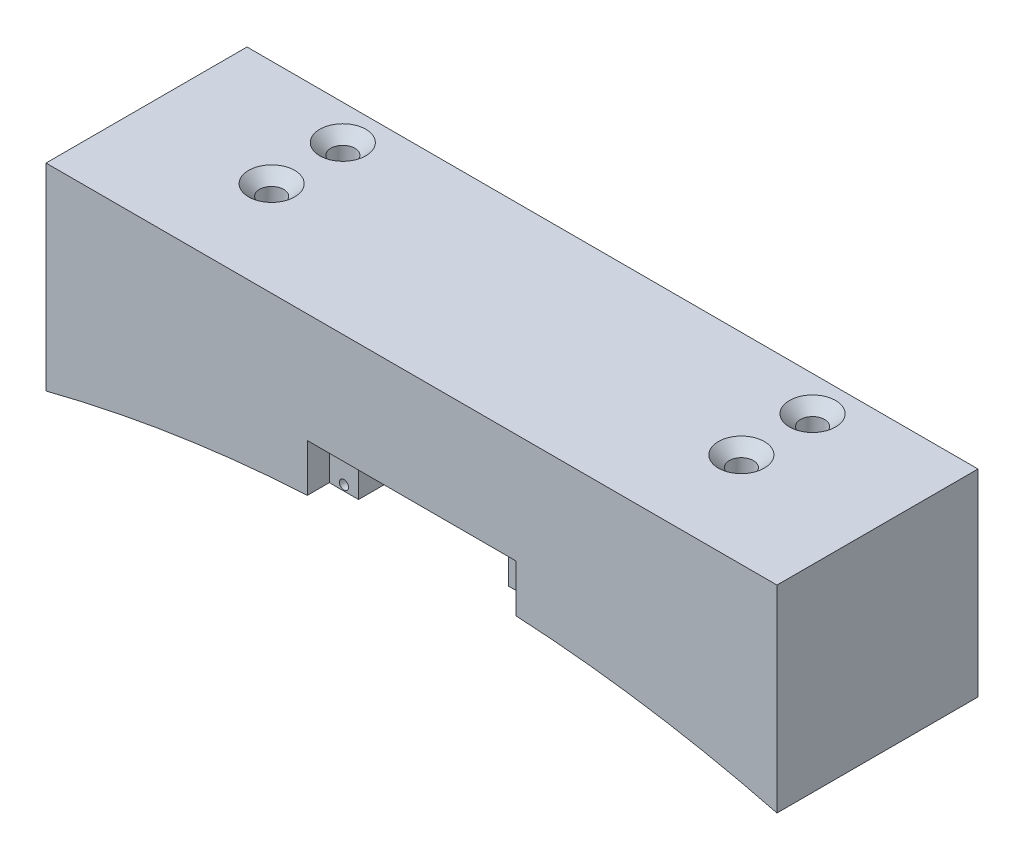
SolidWorks part; units mm, degrees
ref_plane "Front Plane" through (0, 0, 0) normal (0, 0, 1) x (1, 0, 0)
ref_plane "Top Plane" through (0, 0, 0) normal (0, 1, 0) x (1, 0, 0)
ref_plane "Right Plane" through (0, 0, 0) normal (1, 0, 0) x (0, 0, -1)
sketch "Sketch1" plane through (0, 0, 0) normal (0, 1, 0) x (1, 0, 0)
  line L1 (-100, -27.5) -> (100, -27.5)
  line L2 (-100, -27.5) -> (-100, 27.5)
  line L3 (-100, 27.5) -> (100, 27.5)
  line L4 (100, -27.5) -> (100, 27.5)
  line L5 (-100, -27.5) -> (100, 27.5) construction
  line L6 (-100, 27.5) -> (100, -27.5) construction
  point P0 (0, 0)
  dimension "D1" = 200
  dimension "D2" = 55
extrude "Boss-Extrude1" add sketch "Sketch1" along normal blind 30
sketch "Sketch2" plane through (0, 0, 0) normal (0, -1, 0) x (1, 0, 0)
  line L0 (0, 27.5) -> (0, -36.2844) construction
  line L1 (-28.5, 1.4842) -> (-20.5, 1.4842)
  line L2 (-28.5, 1.4842) -> (-28.5, 21.4842)
  line L3 (-28.5, 21.4842) -> (-20.5, 21.4842)
  line L4 (-20.5, 1.4842) -> (-20.5, 21.4842)
  line L5 (-28.5, 1.4842) -> (-20.5, 21.4842) construction
  line L6 (-28.5, 21.4842) -> (-20.5, 1.4842) construction
  line L7 (-100, 27.5) -> (100, 27.5) construction
  line L8 (28.5, 21.4842) -> (20.5, 1.4842) construction
  line L9 (28.5, 1.4842) -> (20.5, 21.4842) construction
  line L10 (20.5, 1.4842) -> (20.5, 21.4842)
  line L11 (28.5, 21.4842) -> (20.5, 21.4842)
  line L12 (28.5, 1.4842) -> (28.5, 21.4842)
  line L13 (28.5, 1.4842) -> (20.5, 1.4842)
  point P0 (-24.5, 11.4842)
  point P14 (24.5, 11.4842)
  dimension "D1" = 8
  dimension "D2" = 20
  dimension "D3" = 20.5
extrude "Boss-Extrude2" add sketch "Sketch2" along normal blind 13
sketch "Sketch4" plane through (0, 0, 21.4842) normal (0, 0, 1) x (1, 0, 0)
  line L0 (-24.5, -13) -> (-24.5, 0) construction
  line L1 (-20.5, -13) -> (-28.5, -13) construction
  line L2 (-20.5, 0) -> (-28.5, 0) construction
  line L3 (24.5, -13) -> (24.5, 0) construction
  line L4 (28.5, -13) -> (20.5, -13) construction
  line L5 (28.5, 0) -> (20.5, 0) construction
sketch "Sketch6" plane through (0, 0, 21.4842) normal (0, 0, 1) x (1, 0, 0)
  line L0 (-28.5, -6.5) -> (-20.5, -6.5) construction
  line L1 (-28.5, -13) -> (-28.5, 0) construction
  line L2 (-20.5, -13) -> (-20.5, 0) construction
  line L3 (20.5, -13) -> (20.5, 0) construction
  line L4 (20.5, -6.5) -> (28.5, -6.5) construction
  line L5 (28.5, -13) -> (28.5, 0) construction
sketch "Sketch7" plane through (0, 0, 21.4842) normal (0, 0, 1) x (1, 0, 0)
  line L0 (-24.5, -13) -> (-24.5, 0) construction
  line L2 (-100, 0) -> (100, 0) construction
  circle A0 centre (-24.5, -1.5) radius 1.25
  circle A1 centre (-24.5, -11.5) radius 1.25
  point P10 (0, 0)
  point P12 (0, 0)
  dimension "D3" = 2.5
  dimension "D4" = 2.5
  dimension "D1" = 10
  dimension "D7" = 1.5
extrude "Cut-Extrude1" cut sketch "Sketch7" against normal through all
sketch "Sketch10" plane through (0, 0, 0) normal (0, -1, 0) x (-1, 0, 0)
  line L0 (0, -27.5) -> (0, 30.005) construction
  line L1 (100, -27.5) -> (-100, -27.5) construction
sketch "Sketch11" plane through (0, 0, 21.4842) normal (0, 0, 1) x (1, 0, 0)
  line L0 (24.5, -13) -> (24.5, 0) construction
  line L1 (28.5, 0) -> (20.5, 0) construction
  circle A0 centre (24.5, -1.5) radius 1.25
  circle A1 centre (24.5, -11.5) radius 1.25
  dimension "D1" = 10
  dimension "D2" = 1.5
extrude "Cut-Extrude2" cut sketch "Sketch11" against normal blind 13
sketch "Sketch13" plane through (0, 0, 0) normal (0, -1, 0) x (1, 0, 0)
  line L0 (100, -27.5) -> (-100, -27.5) construction
  line L1 (-100, 27.5) -> (-28.4968, 27.5)
  line L2 (-100, 27.5) -> (-100, -27.5)
  line L3 (-100, -27.5) -> (-28.4968, -27.5)
  line L4 (-28.4968, 27.5) -> (-28.4968, -27.5)
  line L6 (100, 27.5) -> (28.5439, 27.5)
  line L7 (100, 27.5) -> (100, -27.5)
  line L8 (100, -27.5) -> (28.5439, -27.5)
  line L9 (28.5439, 27.5) -> (28.5439, -27.5)
extrude "Boss-Extrude3" add sketch "Sketch13" along normal blind 13
sketch "Sketch16" plane through (0, -13, 0) normal (0, -1, 0) x (-1, 0, 0)
  line L0 (-64.272, -27.5) -> (-64.272, 31.589) construction
  line L1 (-100, -27.5) -> (-28.5439, -27.5) construction
  line L2 (64.2484, -27.5) -> (64.2484, 31.589) construction
  line L3 (28.4968, -27.5) -> (100, -27.5) construction
  circle A0 centre (-64.272, 17.9587) radius 3
  circle A1 centre (-64.272, -1.5196) radius 3
  circle A2 centre (64.2484, 17.9587) radius 3
  circle A3 centre (64.2484, -1.5196) radius 3
  dimension "D1" = 6
  dimension "D2" = 6
  dimension "D3" = 6
  dimension "D4" = 6
sketch "Sketch24" plane through (0, 0, 27.5) normal (0, 0, 1) x (1, 0, 0)
  line L0 (100, -13) -> (28.5439, -13)
  line L1 (-28.4968, -13) -> (-100, -13)
  arc A2 (-100, -13) -> (-28.4968, -13) centre (-64.2484, -13) cw
  arc A3 (28.5439, -13) -> (100, -13) centre (64.272, -13) cw
sketch "Sketch26" plane through (0, 0, 27.5) normal (0, 0, 1) x (1, 0, 0)
  line L0 (100, -24.0218) -> (100, -13)
  line L1 (0, 0) -> (0, 30) construction
  line L2 (-100, 30) -> (100, 30) construction
  line L3 (100, -13) -> (28.5439, -13)
  line L4 (-100, -24.0218) -> (-100, -13)
  line L5 (-100, -13) -> (-28.5439, -13)
  arc A0 (28.5439, -13) -> (100, -24.0218) centre (8.3729, -380.9147) cw
  arc A1 (-28.5439, -13) -> (-100, -24.0218) centre (-8.3729, -380.9147) ccw
extrude "Boss-Extrude4" add sketch "Sketch26" against normal through all
sketch "Sketch27" plane through (0, 0, 27.5) normal (0, 0, 1) x (1, 0, 0)
  line L0 (0.0235, 0) -> (0, 30) construction
  line L1 (-28.4968, 0) -> (28.5439, 0) construction
  line L2 (-100, 30) -> (100, 30) construction
sketch "Sketch17" plane through (0, 30, 0) normal (0, 1, 0) x (1, 0, 0)
  line L0 (-100, 0) -> (100, 0) construction
  line L1 (-100, 27.5) -> (-100, -27.5) construction
  line L2 (100, -27.5) -> (100, 27.5) construction
sketch "Sketch22" plane through (0, 30, 0) normal (0, 1, 0) x (1, 0, 0)
  circle A0 centre (64.272, 17.9587) radius 3
  circle A1 centre (-64.2484, 17.9587) radius 3
  circle A2 centre (-64.2484, -1.5196) radius 3
  circle A3 centre (64.272, -1.5196) radius 3
hole_wizard "CSK for M6 Flat Head Machine Screw2" positions "3DSketch3" profile "Sketch23" countersink size "M6" standard "ANSI Metric" end condition through all
sketch3d "3DSketch3"
  point P0 (-64.2484, 30, -17.9587)
  point P3 (64.272, 30, -17.9587)
  point P6 (-64.2484, 30, 1.5196)
  point P9 (64.272, 30, 1.5196)
sketch "Sketch23" plane through (-64.2484, 30, -17.9587) normal (1, 0, 0) x (0, 0, 1)
  line L0 (0, 0) -> (0, 54.0218)
  line L1 (0, 54.0218) -> (3.3, 54.0218)
  line L2 (3.3, 54.0218) -> (3.3, 3)
  line L3 (3.3, 3) -> (6.3, 0)
  line L5 (6.3, 0) -> (0, 0)
  line L6 (-3.3, 3) -> (-6.3, 0) construction
  line L11 (0, -6.35) -> (0, 107.95) construction
  dimension "Thru Hole Dia." = 6.6
  dimension "Thru Hole Depth" = 54.0218
  dimension "Near C'Sink Dia." = 12.6
  dimension "Near C'Sink Angle" = 90
